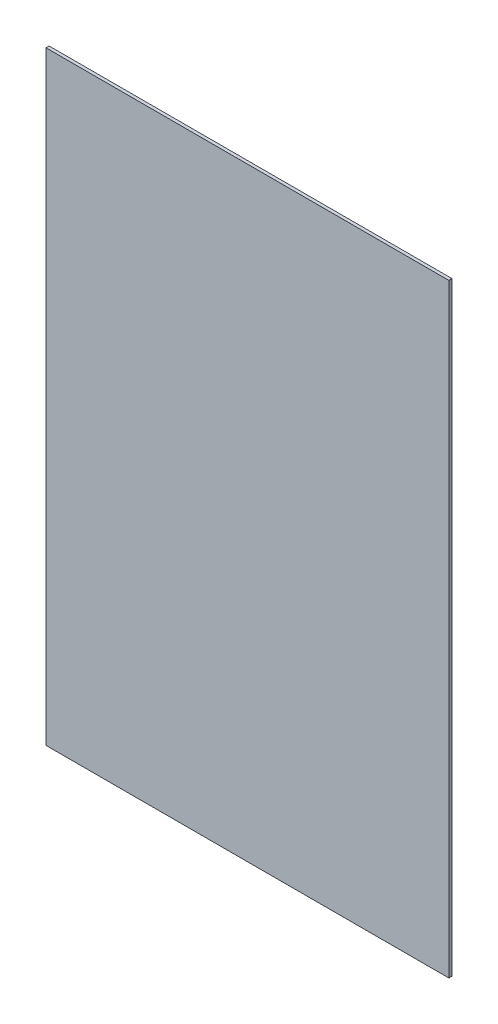
SolidWorks part; units mm, degrees
ref_plane "Front Plane" through (0, 0, 0) normal (0, 0, 1) x (1, 0, 0)
ref_plane "Top Plane" through (0, 0, 0) normal (0, 1, 0) x (1, 0, 0)
ref_plane "Right Plane" through (0, 0, 0) normal (1, 0, 0) x (0, 0, -1)
sketch "Sketch1" plane through (0, 0, 0) normal (0, 0, 1) x (1, 0, 0)
  line L1 (0, 0) -> (609.6, 0)
  line L2 (0, 0) -> (0, 914.4)
  line L3 (0, 914.4) -> (609.6, 914.4)
  line L4 (609.6, 0) -> (609.6, 914.4)
  dimension "D1" = 914.4
  dimension "D2" = 609.6
extrude "Extrude1" add sketch "Sketch1" along normal blind 4.7625
